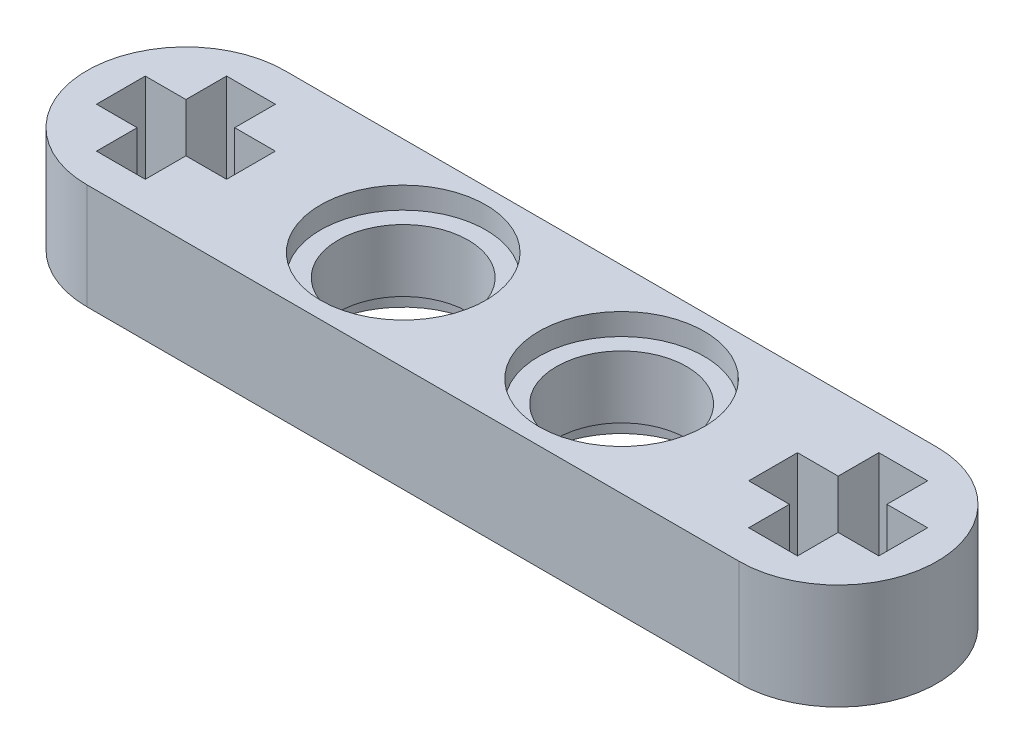
SolidWorks part; units mm, degrees
ref_plane "Front Plane" through (0, 0, 0) normal (0, 0, 1) x (1, 0, 0)
ref_plane "Top Plane" through (0, 0, 0) normal (0, 1, 0) x (1, 0, 0)
ref_plane "Right Plane" through (0, 0, 0) normal (1, 0, 0) x (0, 0, -1)
sketch "Sketch1" plane through (0, 0, 0) normal (0, 1, 0) x (1, 0, 0)
  line L0 (-12.035, 0) -> (12.035, 0) construction
  line L1 (-55, 0) -> (55, 0) construction
  line L2 (-12.035, 3.65) -> (12.035, 3.65)
  line L3 (-12.035, -3.65) -> (12.035, -3.65)
  line L4 (-15.685, 0) -> (-15.685, -5.5699) construction
  line L5 (-14.435, 0) -> (-14.435, -5.5699) construction
  line L6 (11.135, 2.4) -> (11.135, 0.9)
  line L7 (11.135, 2.4) -> (12.935, 2.4)
  line L8 (11.135, -2.4) -> (12.935, -2.4)
  line L9 (12.935, 2.4) -> (12.935, 0.9)
  line L10 (11.135, 2.4) -> (12.935, -2.4) construction
  line L11 (11.135, -2.4) -> (12.935, 2.4) construction
  line L12 (14.435, -0.9) -> (12.935, -0.9)
  line L13 (14.435, -0.9) -> (14.435, 0.9)
  line L14 (9.635, -0.9) -> (9.635, 0.9)
  line L15 (14.435, 0.9) -> (12.935, 0.9)
  line L16 (14.435, -0.9) -> (9.635, 0.9) construction
  line L17 (9.635, -0.9) -> (14.435, 0.9) construction
  line L18 (11.135, 0.9) -> (9.635, 0.9)
  line L19 (11.135, -0.9) -> (9.635, -0.9)
  line L20 (11.135, -0.9) -> (11.135, -2.4)
  line L21 (12.935, -0.9) -> (12.935, -2.4)
  line L34 (-12.9331, 2.4011) -> (-12.9331, 0.9011)
  line L35 (-12.9331, 2.4011) -> (-11.1331, 2.4011)
  line L36 (-12.9331, -2.3989) -> (-11.1331, -2.3989)
  line L37 (-11.1331, 2.4011) -> (-11.1331, 0.9011)
  line L38 (-9.6331, -0.8989) -> (-11.1331, -0.8989)
  line L39 (-9.6331, -0.8989) -> (-9.6331, 0.9011)
  line L40 (-14.4331, -0.8989) -> (-14.4331, 0.9011)
  line L41 (-9.6331, 0.9011) -> (-11.1331, 0.9011)
  line L42 (-12.9331, 0.9011) -> (-14.4331, 0.9011)
  line L43 (-12.9331, -0.8989) -> (-14.4331, -0.8989)
  line L44 (-12.9331, -0.8989) -> (-12.9331, -2.3989)
  line L45 (-11.1331, -0.8989) -> (-11.1331, -2.3989)
  line L46 (-12.9331, 0.9011) -> (-11.1331, -0.8989) construction
  line L47 (-12.0331, 0.0011) -> (-11.1331, 0.9011) construction
  arc A0 (-12.035, 3.65) -> (-12.035, -3.65) centre (-12.035, 0) ccw
  arc A1 (12.035, -3.65) -> (12.035, 3.65) centre (12.035, 0) ccw
  circle A2 centre (-4.0331, 0.018) radius 2.4
  circle A3 centre (4.035, 0.0083) radius 2.4
  point P5 (0, 0)
  point P17 (12.035, 0)
  point P18 (12.035, 0)
  point P29 (15.685, 0)
  point P32 (14.435, 0)
  dimension "D3" = 1.25
  dimension "D5" = 1.8
  dimension "D8" = 7.1
  dimension "D9" = 8.0681
  dimension "D1" = 7.3
  dimension "D2" = 31.37
  dimension "D4" = 1.25
  dimension "D6" = 1.8
  dimension "D7" = 7.1
extrude "Boss-Extrude1" add sketch "Sketch1" along normal blind 3.9
sketch "Sketch2" plane through (0, 3.9, 0) normal (0, 1, 0) x (1, 0, 0)
  circle A0 centre (4.035, 0.0083) radius 3.05
  circle A1 centre (-4.0331, 0.018) radius 3.05
extrude "Cut-Extrude1" cut sketch "Sketch2" against normal blind 0.8
sketch "Sketch3" plane through (0, 0, 0) normal (0, -1, 0) x (-1, 0, 0)
  circle A0 centre (4.0331, 0.018) radius 3.05
  circle A1 centre (-4.035, 0.0083) radius 3.05
extrude "Cut-Extrude2" cut sketch "Sketch3" against normal blind 0.8
